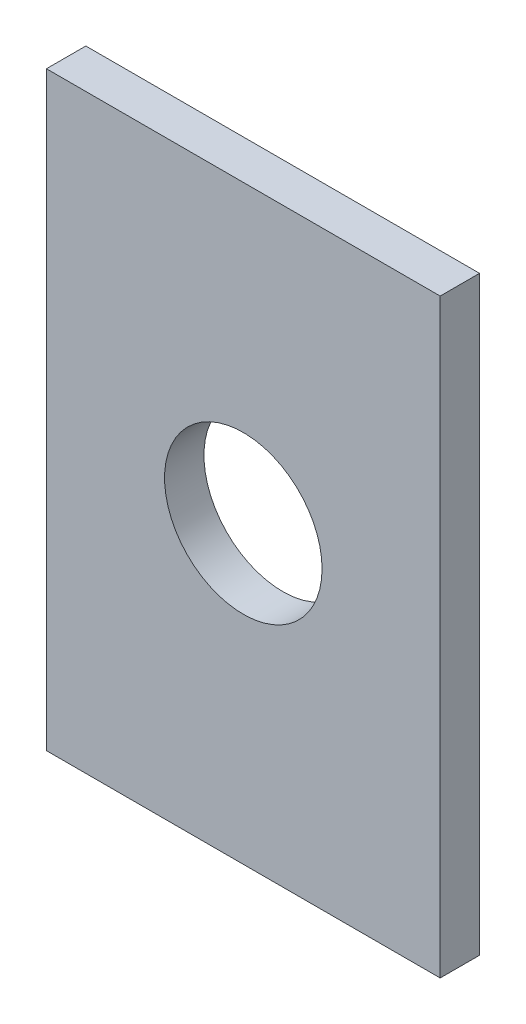
SolidWorks part; units mm, degrees
material "Stal stopowa"
ref_plane "Front Plane" through (0, 0, 0) normal (0, 0, 1) x (1, 0, 0)
ref_plane "Top Plane" through (0, 0, 0) normal (0, 1, 0) x (1, 0, 0)
ref_plane "Right Plane" through (0, 0, 0) normal (1, 0, 0) x (0, 0, -1)
sketch "Szkic1" plane through (0, 0, 0) normal (0, 0, 1) x (1, 0, 0)
  line L1 (0, 0) -> (20, 0)
  line L2 (0, 0) -> (0, 30)
  line L3 (0, 30) -> (20, 30)
  line L4 (20, 0) -> (20, 30)
  circle A0 centre (10, 15) radius 4
  dimension "D3" = 8
  dimension "D5" = 10
  dimension "D1" = 20
  dimension "D2" = 30
  dimension "D4" = 15
extrude "Dodanie-wyciągnięcie1" add sketch "Szkic1" along normal blind 2
